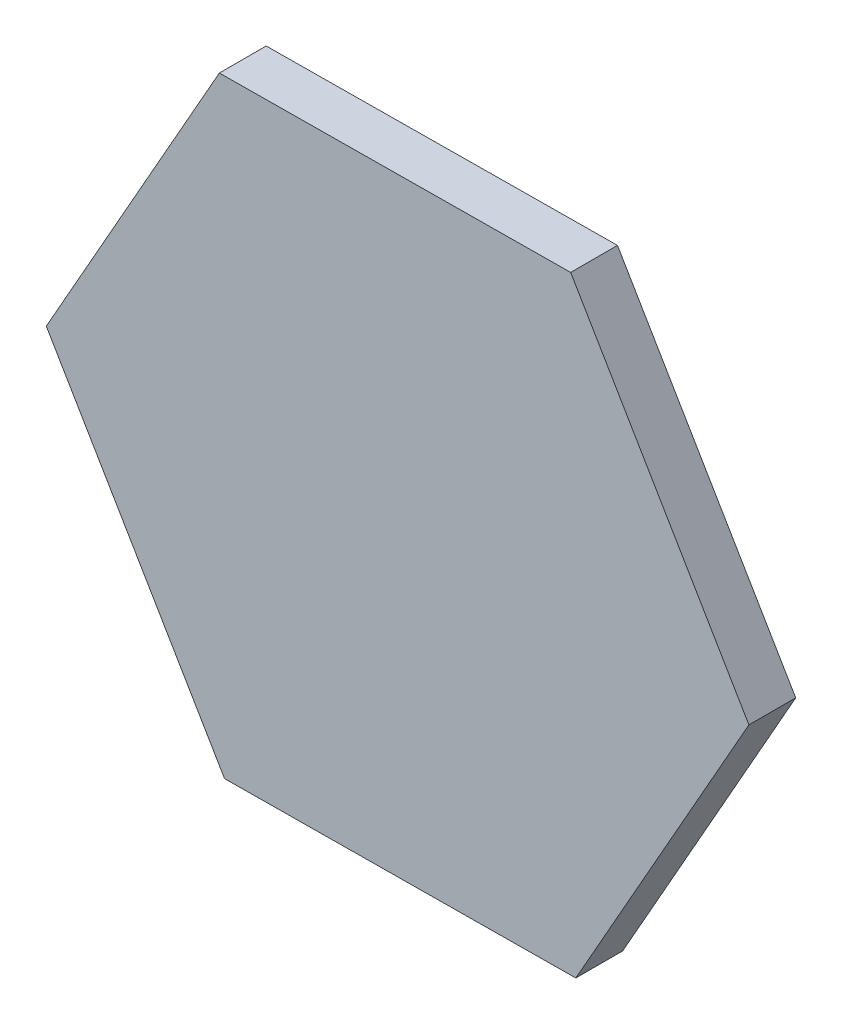
SolidWorks part; units mm, degrees
ref_plane "Alzado" through (0, 0, 0) normal (0, 0, 1) x (1, 0, 0)
ref_plane "Planta" through (0, 0, 0) normal (0, 1, 0) x (1, 0, 0)
ref_plane "Vista lateral" through (0, 0, 0) normal (1, 0, 0) x (0, 0, -1)
sketch "Croquis1" plane through (0, 0, 0) normal (0, 0, 1) x (1, 0, 0)
  line L1 (-3.6974, -6.5316) -> (3.8078, -6.4679)
  line L2 (3.8078, -6.4679) -> (7.5053, 0.0637)
  line L3 (7.5053, 0.0637) -> (3.6974, 6.5316)
  line L4 (3.6974, 6.5316) -> (-3.8078, 6.4679)
  line L5 (-3.8078, 6.4679) -> (-7.5053, -0.0637)
  line L6 (-7.5053, -0.0637) -> (-3.6974, -6.5316)
  circle A0 centre (0, 0) radius 6.5 construction
  dimension "D1" = 13
extrude "Saliente-Extruir1" add sketch "Croquis1" along normal blind 1
